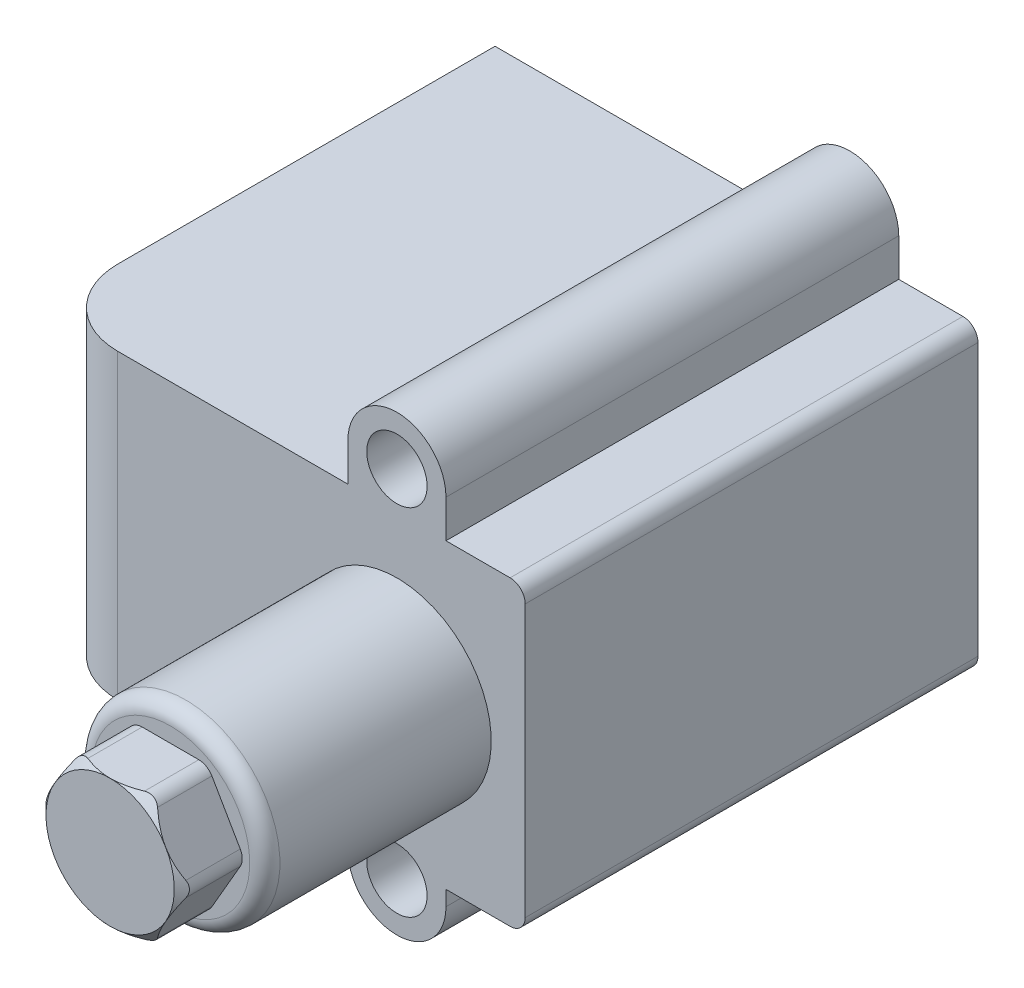
SolidWorks part; units mm, degrees
ref_plane "前视基准面" through (0, 0, 0) normal (0, 0, 1) x (1, 0, 0)
ref_plane "上视基准面" through (0, 0, 0) normal (0, 1, 0) x (1, 0, 0)
ref_plane "右视基准面" through (0, 0, 0) normal (1, 0, 0) x (0, 0, -1)
sketch "草图1" plane through (0, 0, 0) normal (0, 0, 1) x (1, 0, 0)
  line L0 (-64.7568, 0) -> (34.5405, 0) construction
  line L1 (0, 25) -> (0, -22) construction
  line L2 (-6.5, 25) -> (-6.5, 20)
  line L3 (-47, 20) -> (-6.5, 20)
  line L4 (-47, 20) -> (-47, -20)
  line L5 (-47, -20) -> (-6.5, -20)
  line L6 (17, 20) -> (17, -20)
  line L7 (6.5, 25) -> (6.5, 20)
  line L8 (-6.5, -22) -> (-6.5, -20)
  line L9 (6.5, -22) -> (6.5, -20)
  line L10 (6.5, -20) -> (17, -20)
  line L11 (6.5, 20) -> (17, 20)
  circle A0 centre (0, 25) radius 4
  circle A1 centre (0, -22) radius 4
  circle A2 centre (0, 0) radius 5.5
  arc A3 (-6.5, 25) -> (6.5, 25) centre (0, 25) cw
  arc A4 (6.5, -22) -> (-6.5, -22) centre (0, -22) cw
  dimension "D1" = 8
  dimension "D4" = 11
  dimension "D6" = 6.5
  dimension "D2" = 25
  dimension "D3" = 22
  dimension "D5" = 40
  dimension "D7" = 17
  dimension "D8" = 64
extrude "凸台-拉伸1" add sketch "草图1" along normal blind 60
fillet "圆角1" radius 10 1 edges at (-47, 0, 60)
sketch "草图2" plane through (0, 0, 60) normal (0, 0, 1) x (1, 0, 0)
  circle A1 centre (0, 0) radius 12.5
  dimension "D1" = 25
extrude "凸台-拉伸2" add sketch "草图2" along normal offset from surface (30 mm away) 90 up to face at (4, -22, 0)
sketch "草图3" plane through (0, -20, 0) normal (0, -1, 0) x (1, 0, 0)
  line L0 (-37, 60) -> (-6.5, 60) construction
  line L1 (-47, 50) -> (-47, 0) construction
  circle A0 centre (-33, 46) radius 5
  dimension "D3" = 10
  dimension "D1" = 14
  dimension "D2" = 14
hole_wizard "G3/8 螺纹孔1" positions "草图4" profile "草图5" tap size "G3/8" standard "GB"
sketch "草图4" plane through (0, -20, 0) normal (0, -1, 0) x (-1, 0, 0)
  point P0 (33, -46)
sketch "草图5" plane through (-33, -20, 46) normal (1, 0, 0) x (0, 0, -1)
  line L0 (0, 0) -> (0, 14.5816)
  line L1 (0, 14.5816) -> (7.625, 10)
  line L2 (7.625, 10) -> (7.625, 0)
  line L5 (7.625, 0) -> (0, 0)
  line L10 (0, 14.5816) -> (-7.625, 10) construction
  line L11 (0, -6.35) -> (0, 107.95) construction
  dimension "螺纹孔钻头直径" = 15.25
  dimension "螺纹孔钻头深度" = 10
  dimension "导头角度" = 118
cosmetic thread "孔螺蚊线1" parameters "D1"=8, "D2"=16.662
sketch "草图6" plane through (0, 0, 90) normal (0, 0, 1) x (1, 0, 0)
  line L0 (-48.2839, 0) -> (21.7675, 0) construction
  line L2 (9.815, 0) -> (4.9075, 8.5)
  line L3 (4.9075, 8.5) -> (-4.9075, 8.5)
  line L4 (-4.9075, 8.5) -> (-9.815, 0)
  line L5 (-9.815, 0) -> (-4.9075, -8.5)
  line L6 (-4.9075, -8.5) -> (4.9075, -8.5)
  line L7 (4.9075, -8.5) -> (9.815, 0)
  circle A0 centre (0, 0) radius 8.5 construction
  dimension "D1" = 17
extrude "凸台-拉伸3" add sketch "草图6" along normal blind 8
fillet "圆角2" radius 2 3 edges at (-12.5, 0, 90) (17, 20, 30) (17, -20, 30)
fillet "圆角3" radius 2 6 edges at (-4.9075, 8.5, 94) (4.9075, 8.5, 94) (9.815, 0, 94) (4.9075, -8.5, 94) (-4.9075, -8.5, 94) (-9.815, 0, 94)
sketch "草图7" plane through (0, 0, 0) normal (0, 1, 0) x (1, 0, 0)
  line L0 (0, 9.7068) -> (0, -111.2129) construction
  line L1 (-9.5056, -96.9944) -> (-8.5, -98)
  line L2 (-9.5056, -90) -> (-9.5056, -98) construction
  line L3 (-5.4848, -98) -> (-9.2376, -98) construction
  line L4 (-8.5, -98) -> (-9.5056, -98)
  line L5 (-9.5056, -98) -> (-9.2376, -98) construction
  line L6 (-9.5056, -98) -> (-9.5056, -96.9944)
  dimension "D1" = 8.5
revolve "切除-旋转1" cut sketch "草图7" angle 360 about L0
